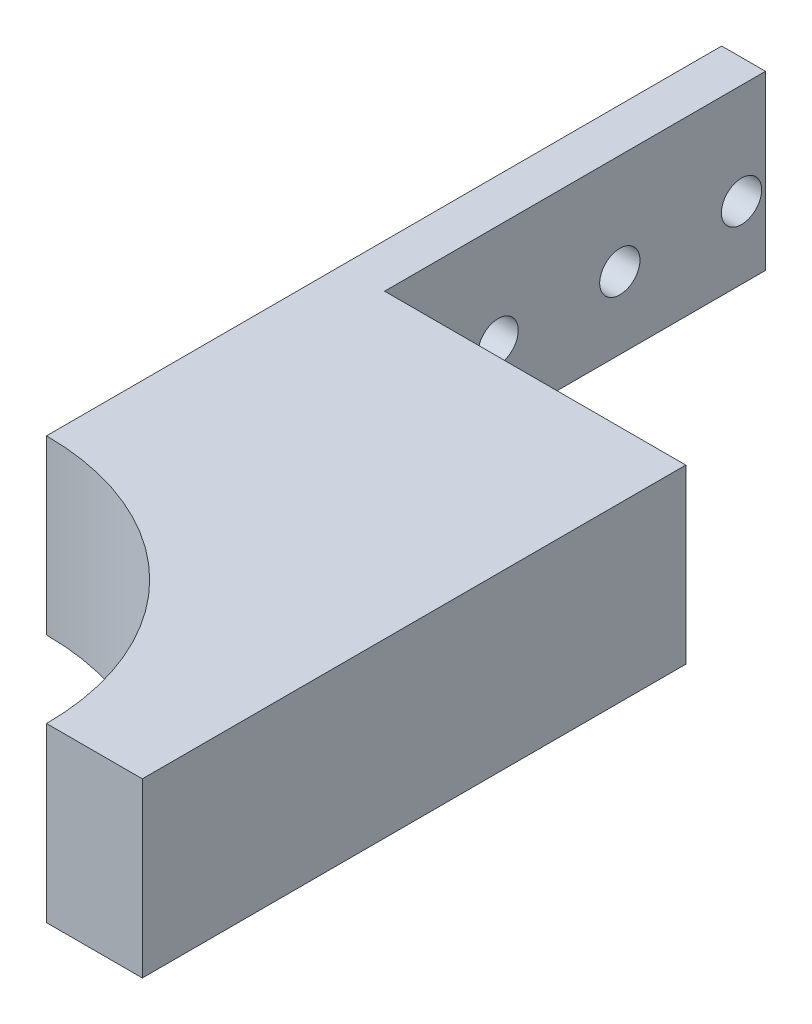
SolidWorks part; units mm, degrees
ref_plane "Front Plane" through (0, 0, 0) normal (0, 0, 1) x (1, 0, 0)
ref_plane "Top Plane" through (0, 0, 0) normal (0, 1, 0) x (1, 0, 0)
ref_plane "Right Plane" through (0, 0, 0) normal (1, 0, 0) x (0, 0, -1)
sketch "Sketch1" plane through (0, 0, 0) normal (0, 1, 0) x (1, 0, 0)
  line L1 (-10, 0) -> (0, 0)
  line L16 (-36, 96.46) -> (-36, 26)
  line L20 (-36, 96.46) -> (-31.43, 96.46)
  line L21 (-31.43, 96.46) -> (-31.43, 56.7121)
  line L22 (-31.43, 56.7121) -> (0, 56.7121)
  line L23 (0, 56.7121) -> (0, 0)
  arc A0 (-36, 26) -> (-10, 0) centre (-36, 0) cw
  dimension "D1" = 31.43
  dimension "D2" = 26
  dimension "D3" = 4.57
  dimension "D4" = 56.7121
  dimension "D5" = 70.46
extrude "Boss-Extrude1" add sketch "Sketch1" along normal blind 18
sketch "Sketch4" plane through (-31.43, 0, 0) normal (1, 0, 0) x (0, 0, -1)
  line L0 (56.7121, 0) -> (96.46, 0) construction
  line L1 (96.46, 18) -> (96.46, 0) construction
  circle A0 centre (81.26, 7.5) radius 2.1
  circle A1 centre (93.96, 7.5) radius 2.1
  circle A2 centre (68.56, 7.5) radius 2.1
  dimension "D5" = 4.2
  dimension "D1" = 12.7
  dimension "D2" = 12.7
  dimension "D3" = 7.5
  dimension "D4" = 2.5
extrude "Cut-Extrude3" cut sketch "Sketch4" against normal blind 10
